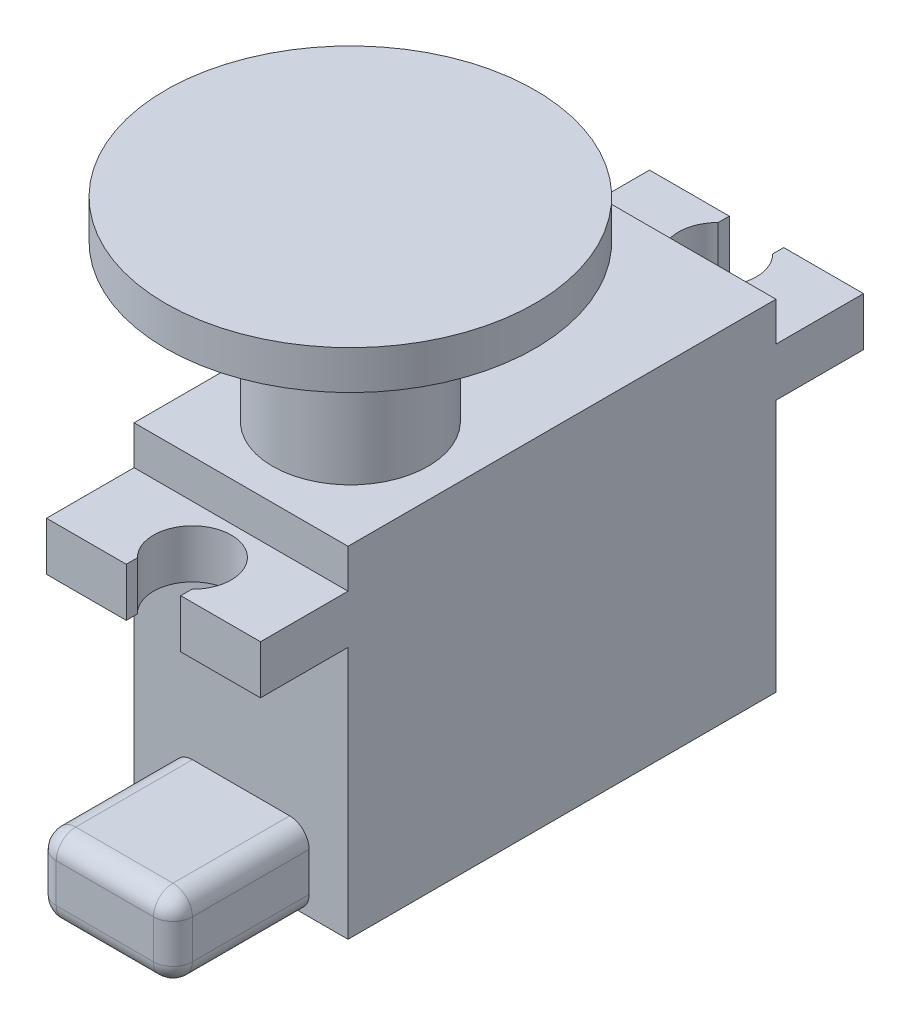
SolidWorks part; units mm, degrees
ref_plane "Front Plane" through (0, 0, 0) normal (0, 0, 1) x (1, 0, 0)
ref_plane "Top Plane" through (0, 0, 0) normal (0, 1, 0) x (1, 0, 0)
ref_plane "Right Plane" through (0, 0, 0) normal (1, 0, 0) x (0, 0, -1)
sketch "Sketch1" plane through (0, 0, 0) normal (0, 1, 0) x (1, 0, 0)
  line L0 (0, 31.1031) -> (0, -30.5994) construction
  line L2 (5.5, -11) -> (-5.5, -11)
  line L3 (5.5, -11) -> (5.5, 11)
  line L4 (5.5, 11) -> (-5.5, 11)
  line L5 (-5.5, -11) -> (-5.5, 11)
  line L6 (5.5, -11) -> (-5.5, 11) construction
  line L7 (5.5, 11) -> (-5.5, -11) construction
  point P1 (0, 0)
extrude "Boss-Extrude1" add sketch "Sketch1" along normal blind 17.5
sketch "Sketch2" plane through (0, 17.5, 0) normal (0, 1, 0) x (1, 0, 0)
  circle A2 centre (0, -5.3802) radius 4
sketch "Sketch8" plane through (0, 0, 11) normal (0, 0, 1) x (1, 0, 0)
  line L0 (-5.5, 17.5) -> (-5.5, 0) construction
  line L1 (-3.5, 0) -> (3.5, 0)
  line L3 (-3.5, 4) -> (3.5, 4)
  line L4 (3.5, 0) -> (3.5, 4)
  line L5 (-3.5, 0) -> (-3.5, 4)
  dimension "D1" = 2
extrude "Boss-Extrude6" add sketch "Sketch8" along normal blind 7
fillet "Fillet1" radius 1 4 edges at (-3.5, 4, 14.5) (3.5, 4, 14.5)
fillet "Fillet2" radius 1 8 edges at (3.2071, 3.7071, 18) (3.2071, 0.2929, 18) (-3.2071, 0.2929, 18) (-3.2071, 3.7071, 18) (-3.5, 2, 18) (0, 0, 18) (3.5, 2, 18) (0, 4, 18)
sketch "Sketch9" plane through (0, 0, 11) normal (0, 0, 1) x (1, 0, 0)
  line L0 (5.5, 17.5) -> (5.5, 0) construction
  line L1 (-5.5, 15.5) -> (5.5, 15.5)
  line L2 (-5.5, 15.5) -> (-5.5, 13)
  line L3 (-5.5, 13) -> (5.5, 13)
  line L4 (5.5, 15.5) -> (5.5, 13)
extrude "Boss-Extrude7" add sketch "Sketch9" along normal blind 4.5
sketch "Sketch10" plane through (0, 0, -11) normal (0, 0, -1) x (-1, 0, 0)
  line L0 (5.5, 17.5) -> (5.5, 0) construction
  line L1 (-5.5, 15.5) -> (5.5, 15.5)
  line L2 (-5.5, 15.5) -> (-5.5, 13)
  line L3 (-5.5, 13) -> (5.5, 13)
  line L4 (5.5, 15.5) -> (5.5, 13)
  dimension "D1" = 2.5
extrude "Boss-Extrude8" add sketch "Sketch10" along normal blind 4.5
sketch "Sketch11" plane through (0, 17.5, 0) normal (0, 1, 0) x (1, 0, 0)
  line L0 (-5.5, 15.5) -> (5.5, 15.5) construction
  line L1 (0, 0) -> (-17.1636, 0) construction
  line L2 (1.4, 15.5) -> (1.4, 14.9283)
  line L3 (1.4, 15.5) -> (-1.4, 15.5)
  line L4 (-1.4, -15.5) -> (-1.4, -14.9283)
  line L5 (1.4, -15.5) -> (1.4, -14.9283)
  line L6 (-1.4, 15.5) -> (-1.4, 14.9283)
  line L7 (1.4, -15.5) -> (-1.4, -15.5)
  arc A0 (1.4, -14.9283) -> (-1.4, -14.9283) centre (0, -13.5) ccw
  arc A2 (-1.4, 14.9283) -> (1.4, 14.9283) centre (0, 13.5) ccw
  dimension "D1" = 2
extrude "Cut-Extrude1" cut sketch "Sketch11" against normal blind 5
extrude "Boss-Extrude9" add sketch "Sketch2" along normal blind 8 contours A2
sketch "Sketch13" plane through (0, 25.5, 0) normal (0, 1, 0) x (1, 0, 0)
  circle A0 centre (0, -5.3802) radius 9.5
extrude "Boss-Extrude10" add sketch "Sketch13" along normal blind 2
